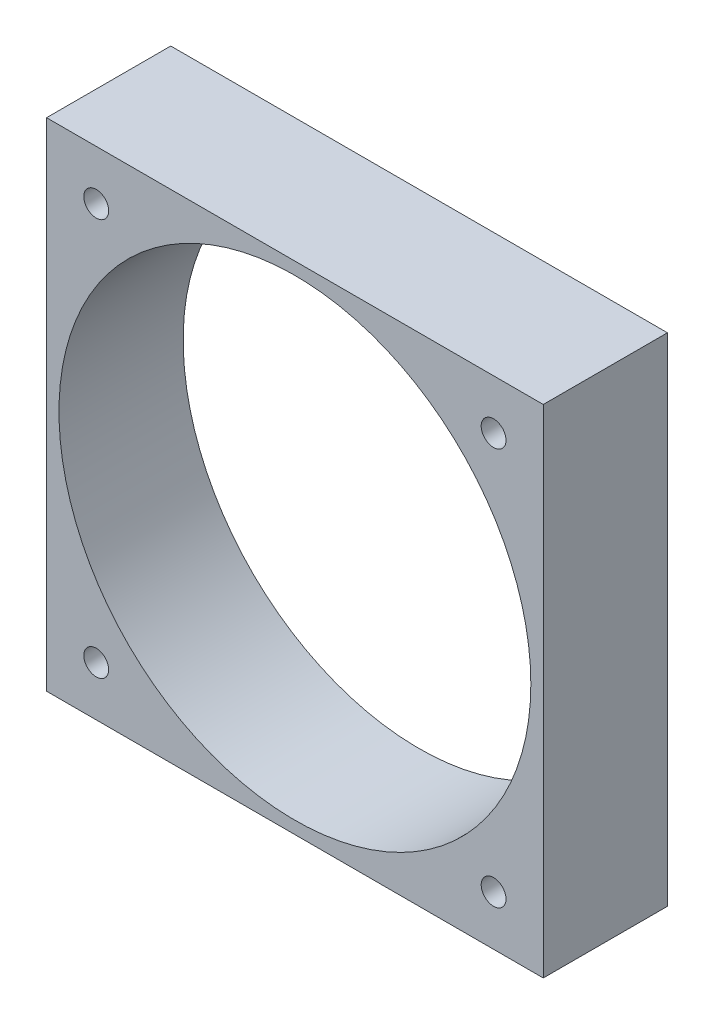
SolidWorks part; units mm, degrees
ref_plane "Front Plane" through (0, 0, 0) normal (0, 0, 1) x (1, 0, 0)
ref_plane "Top Plane" through (0, 0, 0) normal (0, 1, 0) x (1, 0, 0)
ref_plane "Right Plane" through (0, 0, 0) normal (1, 0, 0) x (0, 0, -1)
sketch "Sketch1" plane through (0, 0, 0) normal (0, 0, 1) x (1, 0, 0)
  line L1 (0, 0) -> (40, 0)
  line L2 (0, 0) -> (0, 40)
  line L3 (0, 40) -> (40, 40)
  line L4 (40, 0) -> (40, 40)
  dimension "D1" = 40
  dimension "D2" = 40
extrude "Boss-Extrude1" add sketch "Sketch1" along normal blind 10
sketch "Sketch2" plane through (0, 0, 10) normal (0, 0, 1) x (1, 0, 0)
  line L0 (40, 0) -> (40, 40) construction
  line L1 (4, 36) -> (36, 36)
  line L2 (4, 36) -> (4, 4)
  line L3 (4, 4) -> (36, 4)
  line L4 (36, 36) -> (36, 4)
  line L5 (0, 40) -> (0, 0) construction
  line L6 (0, 0) -> (40, 0) construction
  line L7 (40, 40) -> (0, 40) construction
  circle A0 centre (36, 36) radius 1
  circle A1 centre (4, 36) radius 1
  circle A2 centre (4, 4) radius 1
  circle A3 centre (36, 4) radius 1
  dimension "D5" = 2
  dimension "D1" = 4
  dimension "D2" = 4
  dimension "D3" = 4
  dimension "D4" = 4
extrude "Cut-Extrude1" cut sketch "Sketch2" against normal through all contours A1 | A0 | A3 | A2
sketch "Sketch3" plane through (0, 0, 10) normal (0, 0, 1) x (1, 0, 0)
  circle A0 centre (20, 20) radius 19
  dimension "D1" = 38
extrude "Cut-Extrude2" cut sketch "Sketch3" against normal through all
